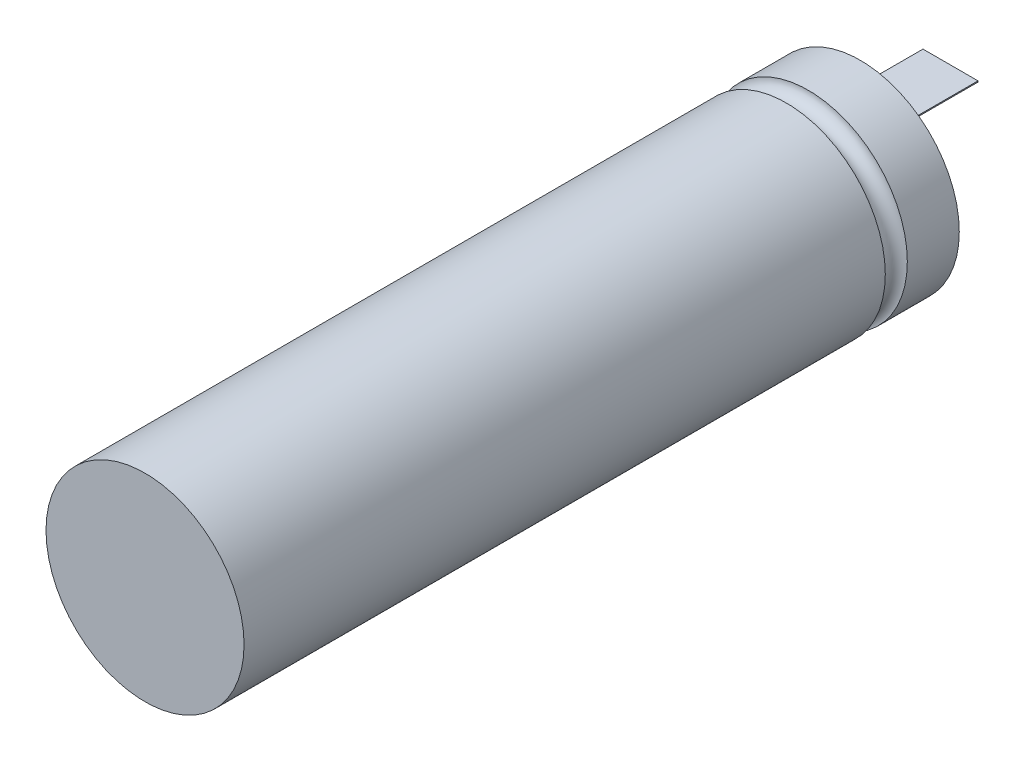
SolidWorks part; units mm, degrees
ref_plane "前视基准面" through (0, 0, 0) normal (0, 0, 1) x (1, 0, 0)
ref_plane "上视基准面" through (0, 0, 0) normal (0, 1, 0) x (1, 0, 0)
ref_plane "右视基准面" through (0, 0, 0) normal (1, 0, 0) x (0, 0, -1)
sketch "草图2" plane through (0, 0, 0) normal (0, 0, 1) x (1, 0, 0)
  circle A0 centre (0, 0) radius 9
  dimension "D1" = 18
extrude "凸台-拉伸1" add sketch "草图2" along normal mid plane 65
sketch "草图3" plane through (0, 0, 0) normal (0, 1, 0) x (1, 0, 0)
  line L0 (-9, 32.5) -> (-9, -32.5) construction
  line L1 (0, 0) -> (0, 20.9209) construction
  circle A0 centre (-9, 26.777) radius 1
  dimension "D1" = 2
revolve "切除-旋转1" cut sketch "草图3" angle 360 about L1
shell "抽壳1" thickness 0.2
sketch "草图4" plane through (0, 0, 32.3) normal (0, 0, -1) x (-1, 0, 0)
  line L0 (0, 4.4738) -> (0, 0) construction
  line L1 (-2.5, 4.5238) -> (2.5, 4.5238)
  line L2 (-2.5, 4.5238) -> (-2.5, 4.4238)
  line L3 (-2.5, 4.4238) -> (2.5, 4.4238)
  line L4 (2.5, 4.5238) -> (2.5, 4.4238)
  line L5 (-2.5, 4.5238) -> (2.5, 4.4238) construction
  line L6 (-2.5, 4.4238) -> (2.5, 4.5238) construction
  point P0 (0, 4.4738)
  dimension "D1" = 5
  dimension "D2" = 0.1
extrude "凸台-拉伸2" add sketch "草图4" along normal blind 73
